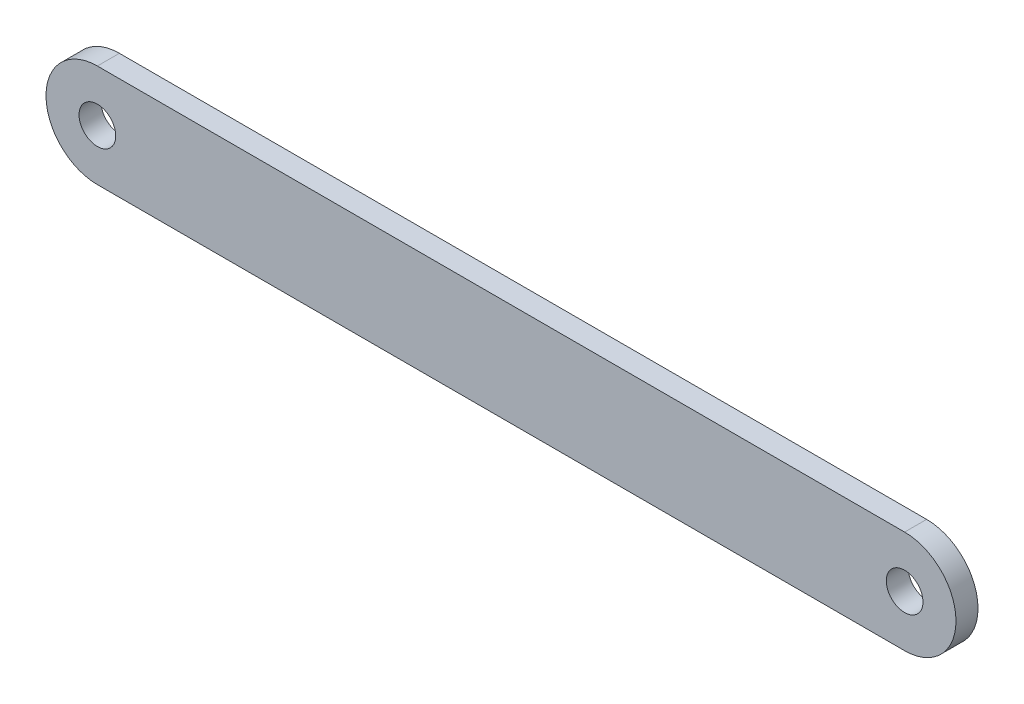
SolidWorks part; units mm, degrees
ref_plane "前视基准面" through (0, 0, 0) normal (0, 0, 1) x (1, 0, 0)
ref_plane "上视基准面" through (0, 0, 0) normal (0, 1, 0) x (1, 0, 0)
ref_plane "右视基准面" through (0, 0, 0) normal (1, 0, 0) x (0, 0, -1)
sketch "Sketch1" plane through (0, 0, 0) normal (0, 0, 1) x (1, 0, 0)
  line L0 (-70.959, 262.1541) -> (39.041, 262.1541) construction
  line L1 (-70.959, 269.1541) -> (39.041, 269.1541)
  line L2 (39.041, 255.1541) -> (-70.959, 255.1541)
  circle A0 centre (-70.959, 262.1541) radius 2.5
  circle A1 centre (39.041, 262.1541) radius 2.5
  circle A2 centre (-70.959, 262.1541) radius 7 construction
  circle A3 centre (39.041, 262.1541) radius 7 construction
  arc A4 (-70.959, 269.1541) -> (-70.959, 255.1541) centre (-70.959, 262.1541) ccw
  arc A5 (39.041, 255.1541) -> (39.041, 269.1541) centre (39.041, 262.1541) ccw
  dimension "D1" = 110
  dimension "D2" = 5
  dimension "D3" = 5
extrude "Boss-Extrude1" add sketch "Sketch1" along normal blind 3
